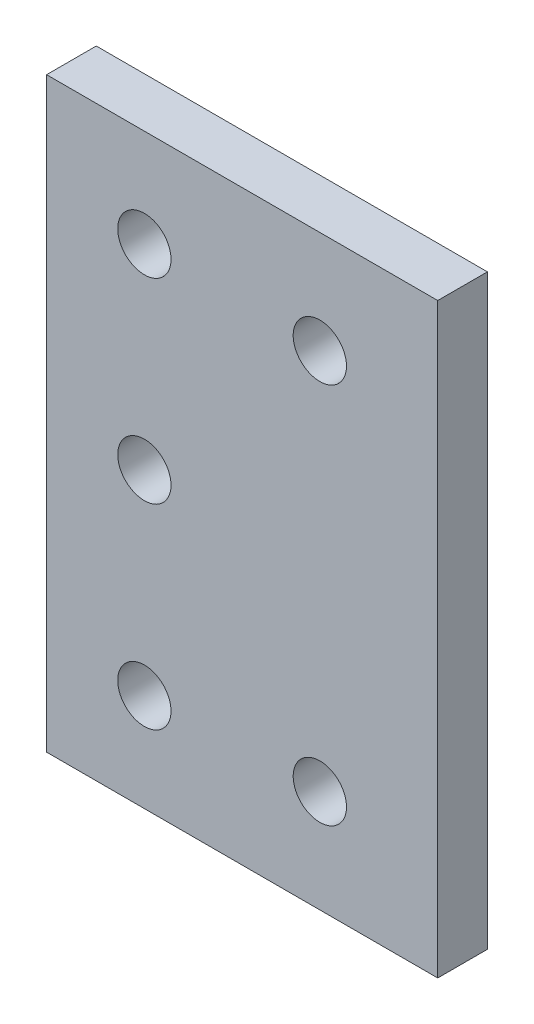
SolidWorks part; units mm, degrees
ref_plane "Front Plane" through (0, 0, 0) normal (0, 0, 1) x (1, 0, 0)
ref_plane "Top Plane" through (0, 0, 0) normal (0, 1, 0) x (1, 0, 0)
ref_plane "Right Plane" through (0, 0, 0) normal (1, 0, 0) x (0, 0, -1)
sketch "Sketch1" plane through (0, 0, 0) normal (0, 0, 1) x (1, 0, 0)
  line L1 (-25, 37.5) -> (25, 37.5)
  line L2 (-25, 37.5) -> (-25, -37.5)
  line L3 (-25, -37.5) -> (25, -37.5)
  line L4 (25, 37.5) -> (25, -37.5)
  point P4 (0, 37.5)
  point P6 (-25, 0)
  dimension "D1" = 75
  dimension "D2" = 50
extrude "Boss-Extrude1" add sketch "Sketch1" along normal blind 6.35
sketch "Sketch2" plane through (0, 0, 6.35) normal (0, 0, 1) x (1, 0, 0)
  line L0 (-25, 37.5) -> (-25, -37.5) construction
  line L1 (25, 37.5) -> (-25, 37.5) construction
  line L2 (-25, -37.5) -> (25, -37.5) construction
  line L3 (25, -37.5) -> (25, 37.5) construction
  circle A0 centre (-12.5, 25) radius 3.405
  circle A1 centre (9.929, 24.4) radius 3.405
  circle A2 centre (-12.5, 0) radius 3.405
  circle A3 centre (-12.5, -25) radius 3.405
  circle A4 centre (9.929, -24.4) radius 3.405
  dimension "D1" = 6.81
  dimension "D2" = 12.5
  dimension "D3" = 12.5
  dimension "D4" = 12.5
  dimension "D5" = 13.1
  dimension "D6" = 15.071
  dimension "D7" = 13.1
extrude "Cut-Extrude1" cut sketch "Sketch2" against normal through all
equation "\"D3@Sketch2\"=\"D2@Sketch2\""
equation "\"D4@Sketch2\"=\"D2@Sketch2\""
